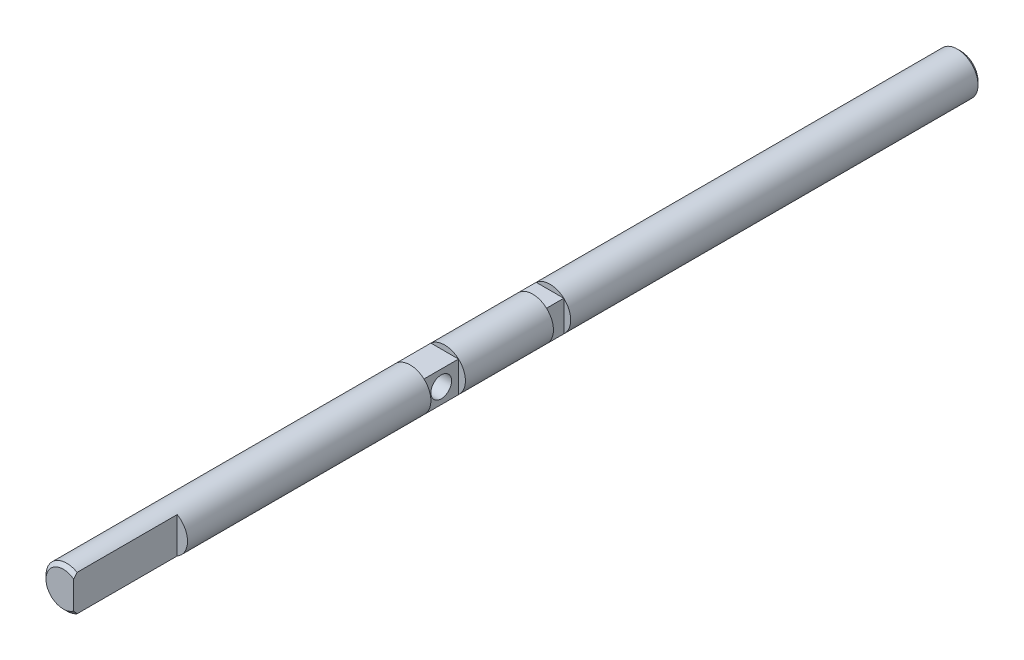
SolidWorks part; units mm, degrees
material "1023 Carbon Steel Sheet (SS)"
ref_plane "Ön Düzlem" through (0, 0, 0) normal (0, 0, 1) x (1, 0, 0)
ref_plane "Üst Düzlem" through (0, 0, 0) normal (0, 1, 0) x (1, 0, 0)
ref_plane "Sağ Düzlem" through (0, 0, 0) normal (1, 0, 0) x (0, 0, -1)
sketch "Sketch1" plane through (0, 0, 0) normal (0, 0, 1) x (1, 0, 0)
  circle A0 centre (0, 0) radius 6
  dimension "D1" = 12
extrude "Boss-Extrude1" add sketch "Sketch1" along normal blind 260
chamfer "Chamfer1" distance 1 angle 45 2 edges at (6, 0, 0) (6, 0, 260)
sketch "Sketch3" plane through (0, 0, 0) normal (0, 1, 0) x (1, 0, 0)
  line L0 (3, -260) -> (3, -230)
  line L1 (-5, -260) -> (5, -260) construction
  line L2 (3, -230) -> (6, -230)
  line L3 (6, -259) -> (6, -1) construction
  line L4 (6, -230) -> (6, -260)
  line L5 (6, -260) -> (3, -260)
  line L6 (6, -149.5) -> (4, -149.5)
  line L7 (4, -149.5) -> (4, -159.5)
  line L8 (4, -159.5) -> (6, -159.5)
  line L9 (6, -159.5) -> (6, -149.5)
  line L10 (-4, -149.5) -> (-6, -149.5)
  line L11 (-6, -1) -> (-6, -259) construction
  line L12 (-6, -149.5) -> (-6, -159.5)
  line L13 (-6, -159.5) -> (-4, -159.5)
  line L14 (-4, -159.5) -> (-4, -149.5)
  line L15 (6, -124) -> (4, -124)
  line L16 (4, -124) -> (4, -119)
  line L17 (4, -119) -> (6, -119)
  line L18 (6, -119) -> (6, -124)
  dimension "D1" = 30
  dimension "D2" = 3
  dimension "D3" = 10
  dimension "D4" = 2
  dimension "D5" = 100.5
  dimension "D6" = 136
  dimension "D7" = 5
extrude "Cut-Extrude1" cut sketch "Sketch3" against normal through all both and the other way through all
sketch "Sketch4" plane through (4, 0, 0) normal (1, 0, 0) x (0, 0, -1)
  line L0 (-159.5, 4.4721) -> (-149.5, -4.4721) construction
  line L1 (-149.5, 4.4721) -> (-159.5, -4.4721) construction
  circle A0 centre (-154.5, 0) radius 3
  dimension "D1" = 6
extrude "Cut-Extrude2" cut sketch "Sketch4" against normal through all both
sketch "Sketch5" plane through (0, 0, 0) normal (1, 0, 0) x (0, 0, -1)
  line L0 (-159.5, 6) -> (-159.5, 4.4721)
  line L1 (-1, 6) -> (-259, 6) construction
  line L2 (-159.5, 4.4721) -> (-149.5, 4.4721)
  line L3 (-149.5, 4.4721) -> (-149.5, 6)
  line L4 (-149.5, 6) -> (-159.5, 6)
  line L5 (-124, 4.4721) -> (-124, 6)
  line L6 (-124, 6) -> (-119, 6)
  line L7 (-119, 6) -> (-119, 4.4721)
  line L8 (-119, 4.4721) -> (-124, 4.4721)
extrude "Cut-Extrude3" cut sketch "Sketch5" against normal through all both and the other way through all
